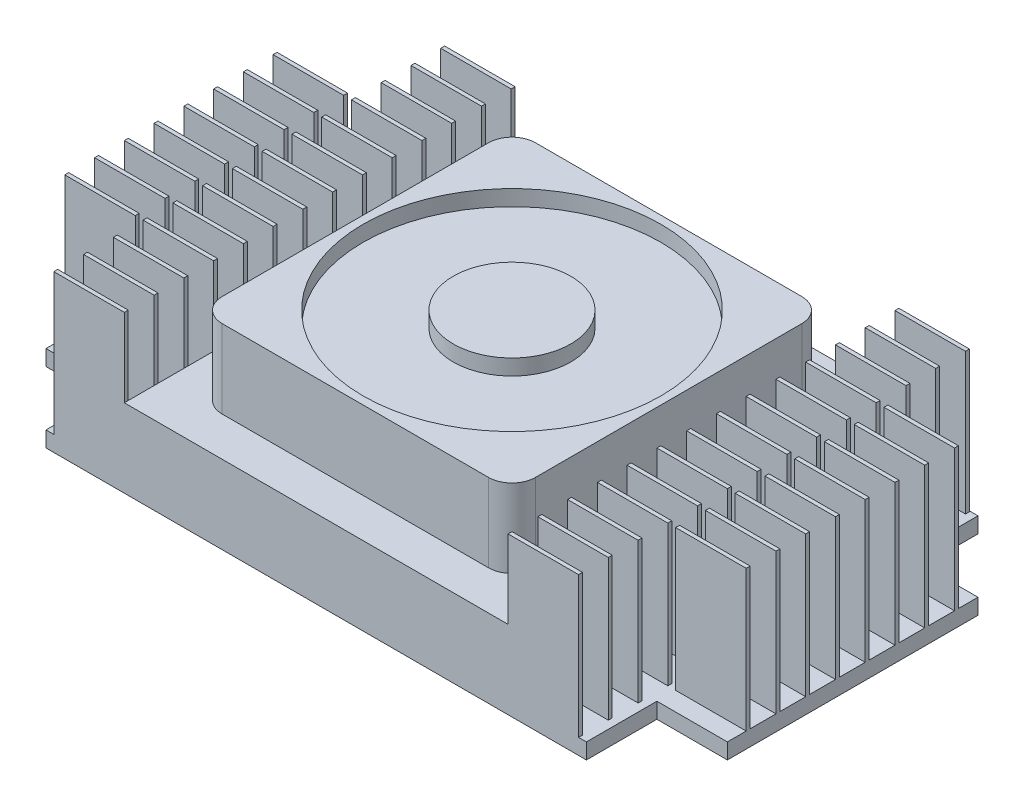
SolidWorks part; units mm, degrees
ref_plane "Front Plane" through (0, 0, 0) normal (0, 0, 1) x (1, 0, 0)
ref_plane "Top Plane" through (0, 0, 0) normal (0, 1, 0) x (1, 0, 0)
ref_plane "Right Plane" through (0, 0, 0) normal (1, 0, 0) x (0, 0, -1)
sketch "Sketch1" plane through (0, 0, 0) normal (0, 1, 0) x (1, 0, 0)
  line L0 (-43.5, 16) -> (-34.5, 16)
  line L1 (-34.5, 25) -> (34.5, 25)
  line L2 (-43.5, 16) -> (-43.5, -16)
  line L3 (-34.5, -25) -> (34.5, -25)
  line L4 (43.5, 16) -> (43.5, -16)
  line L5 (-34.5, 16) -> (-34.5, 25)
  line L6 (34.5, 25) -> (34.5, 16)
  line L7 (34.5, 16) -> (43.5, 16)
  line L8 (43.5, -16) -> (34.5, -16)
  line L9 (34.5, -16) -> (34.5, -25)
  line L10 (-34.5, -25) -> (-34.5, -16)
  line L11 (-34.5, -16) -> (-43.5, -16)
  point P0 (0, 25)
  point P1 (43.5, 0)
  dimension "D1" = 50
  dimension "D2" = 87
  dimension "D3" = 9
extrude "Boss-Extrude1" add sketch "Sketch1" along normal blind 2
sketch "Sketch2" plane through (0, 2, 0) normal (0, 1, 0) x (1, 0, 0)
  line L12 (-24.5, -21.2) -> (-24.5, -20.7)
  line L13 (-33.5, -25) -> (-24.5, -25)
  line L14 (-33.5, -25) -> (-33.5, -24.5)
  line L15 (-33.5, -24.5) -> (-24.5, -24.5)
  line L16 (-24.5, -25) -> (-24.5, -24.5)
  line L17 (-33.5, -20.7) -> (-24.5, -20.7)
  line L18 (-33.5, -21.2) -> (-33.5, -20.7)
  line L19 (-33.5, -21.2) -> (-24.5, -21.2)
  line L20 (-24.5, -17.4) -> (-24.5, -16.9)
  line L21 (-33.5, -16.9) -> (-24.5, -16.9)
  line L22 (-33.5, -17.4) -> (-33.5, -16.9)
  line L23 (-33.5, -17.4) -> (-24.5, -17.4)
  line L24 (-24.5, -13.6) -> (-24.5, -13.1)
  line L25 (-33.5, -13.1) -> (-24.5, -13.1)
  line L26 (-33.5, -13.6) -> (-33.5, -13.1)
  line L27 (-33.5, -13.6) -> (-24.5, -13.6)
  line L28 (-24.5, -9.8) -> (-24.5, -9.3)
  line L29 (-33.5, -9.3) -> (-24.5, -9.3)
  line L30 (-33.5, -9.8) -> (-33.5, -9.3)
  line L31 (-33.5, -9.8) -> (-24.5, -9.8)
  line L32 (-24.5, -6) -> (-24.5, -5.5)
  line L33 (-33.5, -5.5) -> (-24.5, -5.5)
  line L34 (-33.5, -6) -> (-33.5, -5.5)
  line L35 (-33.5, -6) -> (-24.5, -6)
  line L36 (-24.5, -2.2) -> (-24.5, -1.7)
  line L37 (-33.5, -1.7) -> (-24.5, -1.7)
  line L38 (-33.5, -2.2) -> (-33.5, -1.7)
  line L39 (-33.5, -2.2) -> (-24.5, -2.2)
  line L40 (-24.5, 1.6) -> (-24.5, 2.1)
  line L41 (-33.5, 2.1) -> (-24.5, 2.1)
  line L42 (-33.5, 1.6) -> (-33.5, 2.1)
  line L43 (-33.5, 1.6) -> (-24.5, 1.6)
  line L44 (-24.5, 5.4) -> (-24.5, 5.9)
  line L45 (-33.5, 5.9) -> (-24.5, 5.9)
  line L46 (-33.5, 5.4) -> (-33.5, 5.9)
  line L47 (-33.5, 5.4) -> (-24.5, 5.4)
  line L48 (-24.5, 9.2) -> (-24.5, 9.7)
  line L49 (-33.5, 9.7) -> (-24.5, 9.7)
  line L50 (-33.5, 9.2) -> (-33.5, 9.7)
  line L51 (-33.5, 9.2) -> (-24.5, 9.2)
  line L52 (-24.5, 13) -> (-24.5, 13.5)
  line L53 (-33.5, 13.5) -> (-24.5, 13.5)
  line L54 (-33.5, 13) -> (-33.5, 13.5)
  line L55 (-33.5, 13) -> (-24.5, 13)
  line L56 (-24.5, 16.8) -> (-24.5, 17.3)
  line L57 (-33.5, 17.3) -> (-24.5, 17.3)
  line L58 (-33.5, 16.8) -> (-33.5, 17.3)
  line L59 (-33.5, 16.8) -> (-24.5, 16.8)
  line L60 (-24.5, 20.6) -> (-24.5, 21.1)
  line L61 (-33.5, 21.1) -> (-24.5, 21.1)
  line L62 (-33.5, 20.6) -> (-33.5, 21.1)
  line L63 (-33.5, 20.6) -> (-24.5, 20.6)
  line L64 (-24.5, 24.4) -> (-24.5, 24.9)
  line L65 (-33.5, 24.9) -> (-24.5, 24.9)
  line L66 (-33.5, 24.4) -> (-33.5, 24.9)
  line L67 (-33.5, 24.4) -> (-24.5, 24.4)
  line L68 (-34.5, -13.6) -> (-34.5, -13.1)
  line L69 (-43.5, -13.1) -> (-34.5, -13.1)
  line L70 (-43.5, -13.6) -> (-43.5, -13.1)
  line L71 (-43.5, -13.6) -> (-34.5, -13.6)
  line L72 (-34.5, -9.8) -> (-34.5, -9.3)
  line L73 (-43.5, -9.3) -> (-34.5, -9.3)
  line L74 (-43.5, -9.8) -> (-43.5, -9.3)
  line L75 (-43.5, -9.8) -> (-34.5, -9.8)
  line L76 (-34.5, -6) -> (-34.5, -5.5)
  line L77 (-43.5, -5.5) -> (-34.5, -5.5)
  line L78 (-43.5, -6) -> (-43.5, -5.5)
  line L79 (-43.5, -6) -> (-34.5, -6)
  line L80 (-34.5, -2.2) -> (-34.5, -1.7)
  line L81 (-43.5, -1.7) -> (-34.5, -1.7)
  line L82 (-43.5, -2.2) -> (-43.5, -1.7)
  line L83 (-43.5, -2.2) -> (-34.5, -2.2)
  line L84 (-34.5, 1.6) -> (-34.5, 2.1)
  line L85 (-43.5, 2.1) -> (-34.5, 2.1)
  line L86 (-43.5, 1.6) -> (-43.5, 2.1)
  line L87 (-43.5, 1.6) -> (-34.5, 1.6)
  line L88 (-34.5, 5.4) -> (-34.5, 5.9)
  line L89 (-43.5, 5.9) -> (-34.5, 5.9)
  line L90 (-43.5, 5.4) -> (-43.5, 5.9)
  line L91 (-43.5, 5.4) -> (-34.5, 5.4)
  line L92 (-34.5, 9.2) -> (-34.5, 9.7)
  line L93 (-43.5, 9.7) -> (-34.5, 9.7)
  line L94 (-43.5, 9.2) -> (-43.5, 9.7)
  line L95 (-43.5, 9.2) -> (-34.5, 9.2)
  line L96 (-34.5, 13) -> (-34.5, 13.5)
  line L97 (-43.5, 13.5) -> (-34.5, 13.5)
  line L98 (-43.5, 13) -> (-43.5, 13.5)
  line L99 (-43.5, 13) -> (-34.5, 13)
  line L100 (-34.5, -25) -> (34.5, -25) construction
  line L101 (-34.5, -16) -> (-34.5, -25) construction
  line L102 (0, -11) -> (0, 11) construction
  line L103 (43.5, 13) -> (34.5, 13)
  line L104 (43.5, 13) -> (43.5, 13.5)
  line L105 (43.5, 13.5) -> (34.5, 13.5)
  line L106 (34.5, 13) -> (34.5, 13.5)
  line L107 (43.5, 9.2) -> (34.5, 9.2)
  line L108 (43.5, 9.2) -> (43.5, 9.7)
  line L109 (43.5, 9.7) -> (34.5, 9.7)
  line L110 (34.5, 9.2) -> (34.5, 9.7)
  line L111 (43.5, 5.4) -> (34.5, 5.4)
  line L112 (43.5, 5.4) -> (43.5, 5.9)
  line L113 (43.5, 5.9) -> (34.5, 5.9)
  line L114 (34.5, 5.4) -> (34.5, 5.9)
  line L115 (43.5, 1.6) -> (34.5, 1.6)
  line L116 (43.5, 1.6) -> (43.5, 2.1)
  line L117 (43.5, 2.1) -> (34.5, 2.1)
  line L118 (34.5, 1.6) -> (34.5, 2.1)
  line L119 (43.5, -2.2) -> (34.5, -2.2)
  line L120 (43.5, -2.2) -> (43.5, -1.7)
  line L121 (43.5, -1.7) -> (34.5, -1.7)
  line L122 (34.5, -2.2) -> (34.5, -1.7)
  line L123 (43.5, -6) -> (34.5, -6)
  line L124 (43.5, -6) -> (43.5, -5.5)
  line L125 (43.5, -5.5) -> (34.5, -5.5)
  line L126 (34.5, -6) -> (34.5, -5.5)
  line L127 (43.5, -9.8) -> (34.5, -9.8)
  line L128 (43.5, -9.8) -> (43.5, -9.3)
  line L129 (43.5, -9.3) -> (34.5, -9.3)
  line L130 (34.5, -9.8) -> (34.5, -9.3)
  line L131 (43.5, -13.6) -> (34.5, -13.6)
  line L132 (43.5, -13.6) -> (43.5, -13.1)
  line L133 (43.5, -13.1) -> (34.5, -13.1)
  line L134 (34.5, -13.6) -> (34.5, -13.1)
  line L135 (33.5, 24.4) -> (24.5, 24.4)
  line L136 (33.5, 24.4) -> (33.5, 24.9)
  line L137 (33.5, 24.9) -> (24.5, 24.9)
  line L138 (24.5, 24.4) -> (24.5, 24.9)
  line L139 (33.5, 20.6) -> (24.5, 20.6)
  line L140 (33.5, 20.6) -> (33.5, 21.1)
  line L141 (33.5, 21.1) -> (24.5, 21.1)
  line L142 (24.5, 20.6) -> (24.5, 21.1)
  line L143 (33.5, 16.8) -> (24.5, 16.8)
  line L144 (33.5, 16.8) -> (33.5, 17.3)
  line L145 (33.5, 17.3) -> (24.5, 17.3)
  line L146 (24.5, 16.8) -> (24.5, 17.3)
  line L147 (33.5, 13) -> (24.5, 13)
  line L148 (33.5, 13) -> (33.5, 13.5)
  line L149 (33.5, 13.5) -> (24.5, 13.5)
  line L150 (24.5, 13) -> (24.5, 13.5)
  line L151 (33.5, 9.2) -> (24.5, 9.2)
  line L152 (33.5, 9.2) -> (33.5, 9.7)
  line L153 (33.5, 9.7) -> (24.5, 9.7)
  line L154 (24.5, 9.2) -> (24.5, 9.7)
  line L155 (33.5, 5.4) -> (24.5, 5.4)
  line L156 (33.5, 5.4) -> (33.5, 5.9)
  line L157 (33.5, 5.9) -> (24.5, 5.9)
  line L158 (24.5, 5.4) -> (24.5, 5.9)
  line L159 (33.5, 1.6) -> (24.5, 1.6)
  line L160 (33.5, 1.6) -> (33.5, 2.1)
  line L161 (33.5, 2.1) -> (24.5, 2.1)
  line L162 (24.5, 1.6) -> (24.5, 2.1)
  line L163 (33.5, -2.2) -> (24.5, -2.2)
  line L164 (33.5, -2.2) -> (33.5, -1.7)
  line L165 (33.5, -1.7) -> (24.5, -1.7)
  line L166 (24.5, -2.2) -> (24.5, -1.7)
  line L167 (33.5, -6) -> (24.5, -6)
  line L168 (33.5, -6) -> (33.5, -5.5)
  line L169 (33.5, -5.5) -> (24.5, -5.5)
  line L170 (24.5, -6) -> (24.5, -5.5)
  line L171 (33.5, -9.8) -> (24.5, -9.8)
  line L172 (33.5, -9.8) -> (33.5, -9.3)
  line L173 (33.5, -9.3) -> (24.5, -9.3)
  line L174 (24.5, -9.8) -> (24.5, -9.3)
  line L175 (33.5, -13.6) -> (24.5, -13.6)
  line L176 (33.5, -13.6) -> (33.5, -13.1)
  line L177 (33.5, -13.1) -> (24.5, -13.1)
  line L178 (24.5, -13.6) -> (24.5, -13.1)
  line L179 (33.5, -17.4) -> (24.5, -17.4)
  line L180 (33.5, -17.4) -> (33.5, -16.9)
  line L181 (33.5, -16.9) -> (24.5, -16.9)
  line L182 (24.5, -17.4) -> (24.5, -16.9)
  line L183 (33.5, -21.2) -> (24.5, -21.2)
  line L184 (33.5, -21.2) -> (33.5, -20.7)
  line L185 (33.5, -20.7) -> (24.5, -20.7)
  line L186 (24.5, -25) -> (24.5, -24.5)
  line L187 (33.5, -24.5) -> (24.5, -24.5)
  line L188 (33.5, -25) -> (33.5, -24.5)
  line L189 (33.5, -25) -> (24.5, -25)
  line L190 (24.5, -21.2) -> (24.5, -20.7)
  dimension "D1" = 9
  dimension "D2" = 0.5
  dimension "D5" = 1
  dimension "D3" = 14
  dimension "D4" = 2
extrude "Boss-Extrude2" add sketch "Sketch2" along normal blind 18
sketch "Sketch3" plane through (0, 2, 0) normal (0, 1, 0) x (1, 0, 0)
  line L0 (34.5, 25) -> (-34.5, 25) construction
  line L1 (-24.5, -25) -> (24.5, -25)
  line L2 (-24.5, -25) -> (-24.5, 25)
  line L3 (-24.5, 25) -> (24.5, 25)
  line L4 (24.5, -25) -> (24.5, 25)
  line L5 (24.5, 24.9) -> (24.5, 24.4) construction
extrude "Boss-Extrude3" add sketch "Sketch3" along normal blind 8
sketch "Sketch4" plane through (0, 10, 0) normal (0, 1, 0) x (1, 0, 0)
  line L1 (-20, 20) -> (20, 20)
  line L2 (-20, 20) -> (-20, -20)
  line L3 (-20, -20) -> (20, -20)
  line L4 (20, 20) -> (20, -20)
  point P4 (0, 20)
  point P6 (20, 0)
  dimension "D1" = 40
extrude "Boss-Extrude4" add sketch "Sketch4" along normal blind 10
fillet "Fillet1" radius 3 4 edges at (-20, 15, -20) (20, 15, -20) (20, 15, 20) (-20, 15, 20)
sketch "Sketch5" plane through (0, 20, 0) normal (0, 1, 0) x (1, 0, 0)
  circle A0 centre (0, 0) radius 19
  circle A1 centre (0, 0) radius 7.5
  dimension "D1" = 38
  dimension "D2" = 15
extrude "Cut-Extrude1" cut sketch "Sketch5" against normal blind 2
